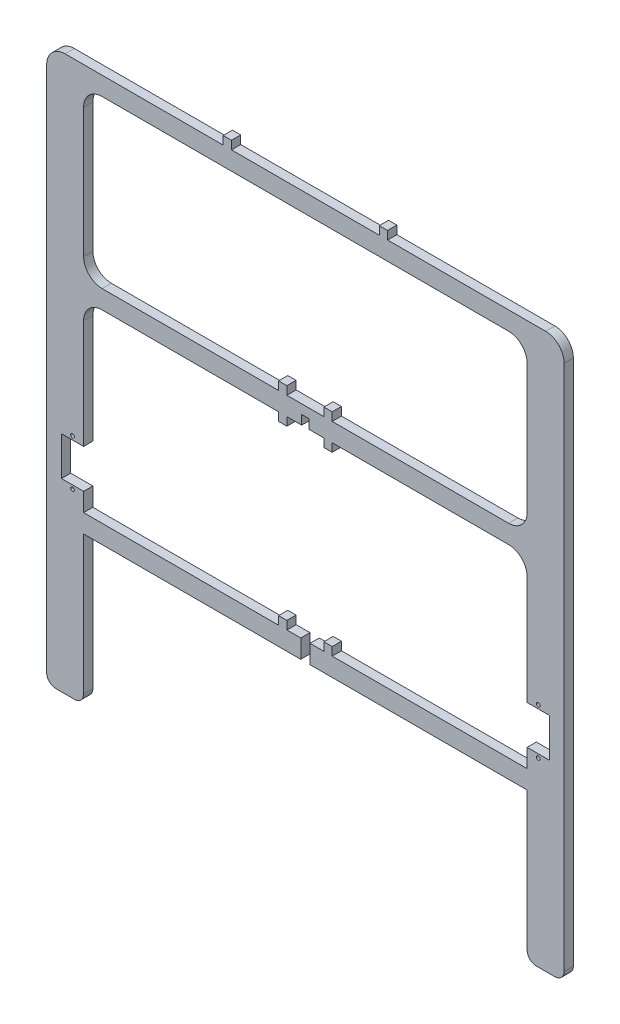
SolidWorks part; units mm, degrees
ref_plane "Front Plane" through (0, 0, 0) normal (0, 0, 1) x (1, 0, 0)
ref_plane "Top Plane" through (0, 0, 0) normal (0, 1, 0) x (1, 0, 0)
ref_plane "Right Plane" through (0, 0, 0) normal (1, 0, 0) x (0, 0, -1)
sketch "Sketch1" plane through (0, 0, 0) normal (0, 0, 1) x (1, 0, 0)
  line L0 (-120, -20) -> (-120, -79)
  line L1 (-130, 100) -> (-120, 100)
  line L2 (-140, 90) -> (-140, -195)
  line L3 (-135, -200) -> (-125, -200)
  line L4 (-120, 80) -> (-120, 10)
  line L5 (-120, 100) -> (0, 100)
  line L6 (-120, -100) -> (-120, -195)
  line L7 (-110, 90) -> (0, 90)
  line L8 (0, 100) -> (0, 90)
  line L9 (-110, 0) -> (-2, 0)
  line L10 (-132, -79) -> (-120, -79)
  line L11 (-110, -10) -> (0, -10)
  line L12 (0, -5) -> (0, -10)
  line L13 (-132, -79) -> (-132, -100)
  line L14 (-2, 0) -> (-2, -5)
  line L15 (-2, -5) -> (0, -5)
  line L16 (-132, -100) -> (-120, -100)
  line L17 (-10, -14.5) -> (-10, -10)
  line L18 (-120, -110) -> (-2.5, -110)
  line L19 (-120, -110) -> (-120, -120)
  line L20 (-120, -120) -> (-2.5, -120)
  line L21 (-2.5, -110) -> (-2.5, -120)
  line L22 (-44.5, 104.5) -> (-40, 104.5)
  line L23 (-44.5, 104.5) -> (-44.5, 100)
  line L24 (-44.5, 100) -> (-40, 100)
  line L25 (-40, 104.5) -> (-40, 100)
  line L26 (-14.5, 4.5) -> (-10, 4.5)
  line L27 (-14.5, 4.5) -> (-14.5, 0)
  line L28 (-14.5, 0) -> (-10, 0)
  line L29 (-10, 4.5) -> (-10, 0)
  line L30 (-14.5, -10) -> (-10, -10)
  line L31 (-14.5, -14.5) -> (-14.5, -10)
  line L32 (-14.5, -14.5) -> (-10, -14.5)
  line L33 (-132, -89.5) -> (-120, -89.5) construction
  line L35 (-14.5, -105.5) -> (-10, -105.5)
  line L36 (-14.5, -105.5) -> (-14.5, -110)
  line L37 (-14.5, -110) -> (-10, -110)
  line L38 (-10, -105.5) -> (-10, -110)
  line L39 (-2, 0) -> (0, 0)
  line L40 (-2, 0) -> (-2, -5)
  line L41 (-2, -5) -> (0, -5)
  line L42 (0, 0) -> (0, -5)
  line L43 (0, -5) -> (-2, -5)
  line L44 (0, -5) -> (0, -10)
  line L45 (0, -10) -> (-2, -10)
  line L46 (-2, -5) -> (-2, -10)
  arc A0 (-130, 100) -> (-140, 90) centre (-130, 90) ccw
  arc A1 (-120, 80) -> (-110, 90) centre (-110, 80) cw
  arc A2 (-110, 0) -> (-120, 10) centre (-110, 10) cw
  arc A3 (-120, -20) -> (-110, -10) centre (-110, -20) cw
  arc A4 (-125, -200) -> (-120, -195) centre (-125, -195) ccw
  arc A5 (-140, -195) -> (-135, -200) centre (-135, -195) ccw
  circle A6 centre (-126, -77) radius 1
  circle A7 centre (-126, -102) radius 1
  point P16 (-140, 100)
  point P27 (-140, -200)
  dimension "D13" = 10
  dimension "D14" = 10
  dimension "D15" = 10
  dimension "D16" = 10
  dimension "D17" = 5
  dimension "D30" = 2
  dimension "D1" = 300
  dimension "D2" = 20
  dimension "D3" = 10
  dimension "D4" = 120
  dimension "D5" = 10
  dimension "D6" = 100
  dimension "D7" = 0
  dimension "D8" = 0
  dimension "D9" = 0
  dimension "D10" = 5
  dimension "D11" = 2
  dimension "D12" = 20
  dimension "D18" = 12
  dimension "D19" = 21
  dimension "D20" = 100
  dimension "D21" = 10
  dimension "D22" = 2.5
  dimension "D23" = 80
  dimension "D24" = 4.5
  dimension "D25" = 4.5
  dimension "D26" = 40
  dimension "D27" = 4.5
  dimension "D28" = 4.5
  dimension "D29" = 10
  dimension "D31" = 2
  dimension "D32" = 6
  dimension "D33" = 10.5
  dimension "D34" = 4.5
  dimension "D35" = 4.5
  dimension "D36" = 10
extrude "Boss-Extrude1" add sketch "Sketch1" along normal mid plane 5 contours L2 A5 L3 A4 L6 L16 L13 L10 L0 A3 L11 L46 L14 L9 A2 L4 A1 L7 L8 L5 L1 A0 A6 A7 | L25 L22 L23 L5 | L29 L26 L27 L9 | L31 L32 L17 L11 | L42 L39 L14 L15 | L21 L18 L6 L20 | L35 L38 L37 L36
mirror "Mirror1" about plane through (0, 0, 0) normal (1, 0, 0) of bodies 112
equation "\"D32@Sketch1\"=(\"D18@Sketch1\")/2"
equation "\"D33@Sketch1\"=(\"D19@Sketch1\")/2"
equation "\"D34@Sketch1\"=\"D27@Sketch1\""
equation "\"D35@Sketch1\"=\"D28@Sketch1\""
equation "\"D36@Sketch1\"=\"D29@Sketch1\""
